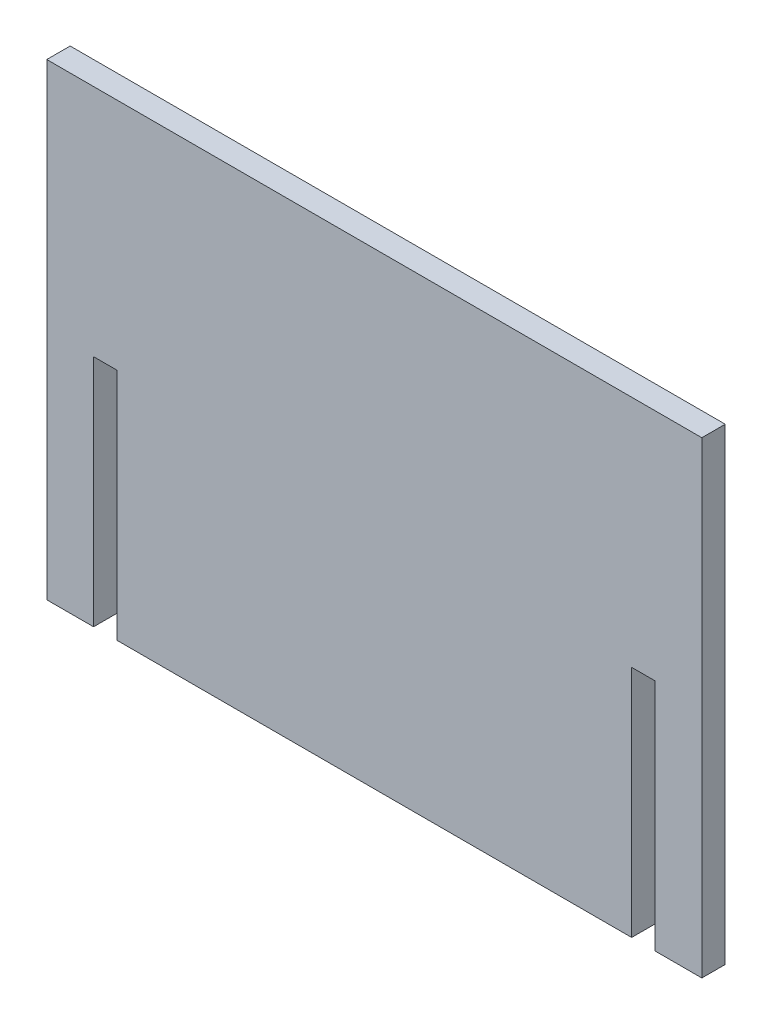
SolidWorks part; units mm, degrees
ref_plane "Front Plane" through (0, 0, 0) normal (0, 0, 1) x (1, 0, 0)
ref_plane "Top Plane" through (0, 0, 0) normal (0, 1, 0) x (1, 0, 0)
ref_plane "Right Plane" through (0, 0, 0) normal (1, 0, 0) x (0, 0, -1)
sketch "Sketch1" plane through (0, 0, 0) normal (0, 0, 1) x (1, 0, 0)
  line L7 (1294.204, -519.4799) -> (1294.204, -532.1799) construction
  line L8 (1294.204, -24.1799) -> (1649.804, -24.1799)
  line L9 (1294.204, -24.1799) -> (1294.204, -278.1799)
  line L11 (1649.804, -24.1799) -> (1649.804, -278.1799)
  line L12 (1649.804, -519.4799) -> (1649.804, -532.1799) construction
  line L13 (1332.304, -24.1799) -> (1319.604, -24.1799) construction
  line L14 (1294.204, -278.1799) -> (1319.604, -278.1799)
  line L15 (1319.604, -24.1799) -> (1319.604, -519.4799) construction
  line L16 (1319.604, -278.1799) -> (1319.604, -151.1799)
  line L17 (1319.604, -151.1799) -> (1332.304, -151.1799)
  line L18 (1332.304, -24.1799) -> (1332.304, -519.4799) construction
  line L19 (1332.304, -151.1799) -> (1332.304, -278.1799)
  line L20 (1332.304, -278.1799) -> (1611.704, -278.1799)
  line L21 (1611.704, -24.1799) -> (1611.704, -519.4799) construction
  line L22 (1611.704, -278.1799) -> (1611.704, -151.1799)
  line L23 (1611.704, -151.1799) -> (1624.404, -151.1799)
  line L24 (1624.404, -24.1799) -> (1624.404, -519.4799) construction
  line L25 (1624.404, -151.1799) -> (1624.404, -278.1799)
  line L26 (1624.404, -278.1799) -> (1649.804, -278.1799)
  dimension "D1" = 127
  dimension "D2" = 254
extrude "Boss-Extrude1" add sketch "Sketch1" along normal mid plane 12.7
